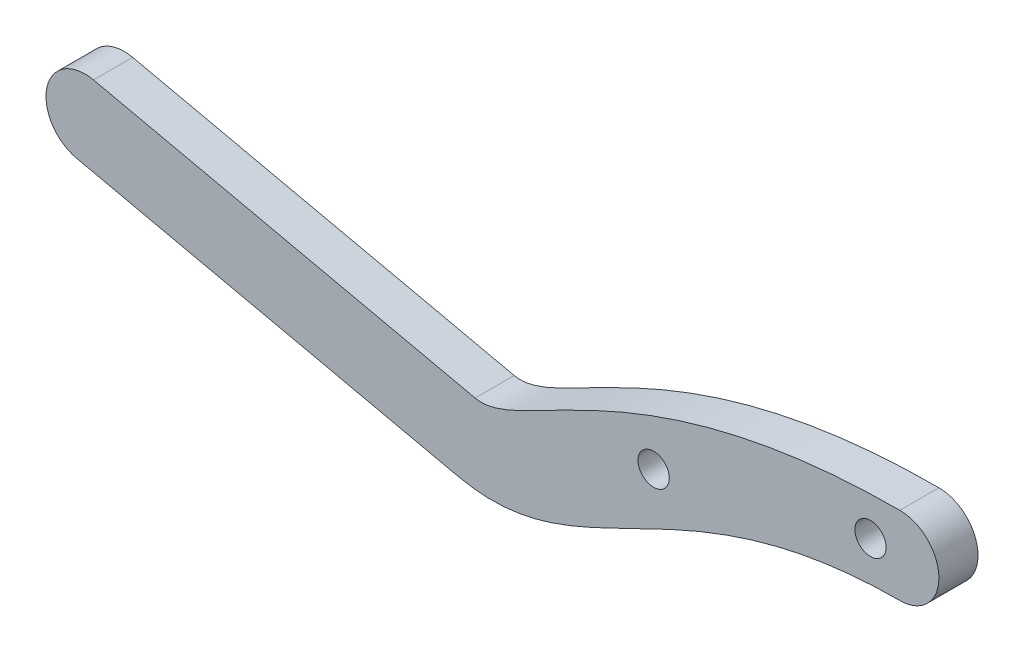
SolidWorks part; units mm, degrees
ref_plane "Front Plane" through (0, 0, 0) normal (0, 0, 1) x (1, 0, 0)
ref_plane "Top Plane" through (0, 0, 0) normal (0, 1, 0) x (1, 0, 0)
ref_plane "Right Plane" through (0, 0, 0) normal (1, 0, 0) x (0, 0, -1)
sketch "Sketch1" plane through (0, 0, 0) normal (0, 0, 1) x (1, 0, 0)
  line L0 (-81.2412, -6.924) -> (-42.1922, -15.5944)
  line L1 (-79.5072, 0.8858) -> (-40.4581, -7.7846)
  circle A0 centre (-22.1922, -4.9562) radius 1.6
  circle A1 centre (0, 0) radius 1.6
  arc A2 (3, -4) -> (3, 4) centre (3, 0) ccw
  arc A5 (-81.2412, -6.924) -> (-79.5072, 0.8858) centre (-80.3742, -3.0191) cw
  spline S0 degree 3 poles (-42.1922, -15.5944) (-29.0423, -18.5142) (-20.6712, -4) (3, -4) knots 0 0 0 0 1 1 1 1
  spline S1 degree 3 poles (-40.4581, -7.7846) (-35.5218, -8.8807) (-24.5851, 4) (3, 4) knots 0 0 0 0 1 1 1 1
  dimension "D2" = 3.2
  dimension "D9" = 3
  dimension "D1" = 40
  dimension "D3" = 20
  dimension "D4" = 10.6382
  dimension "D5" = 22.1922
  dimension "D6" = 4.9562
  dimension "D7" = 8
  dimension "D8" = 8
  dimension "D10" = 6.7205
extrude "Boss-Extrude1" add sketch "Sketch1" along normal blind 4
